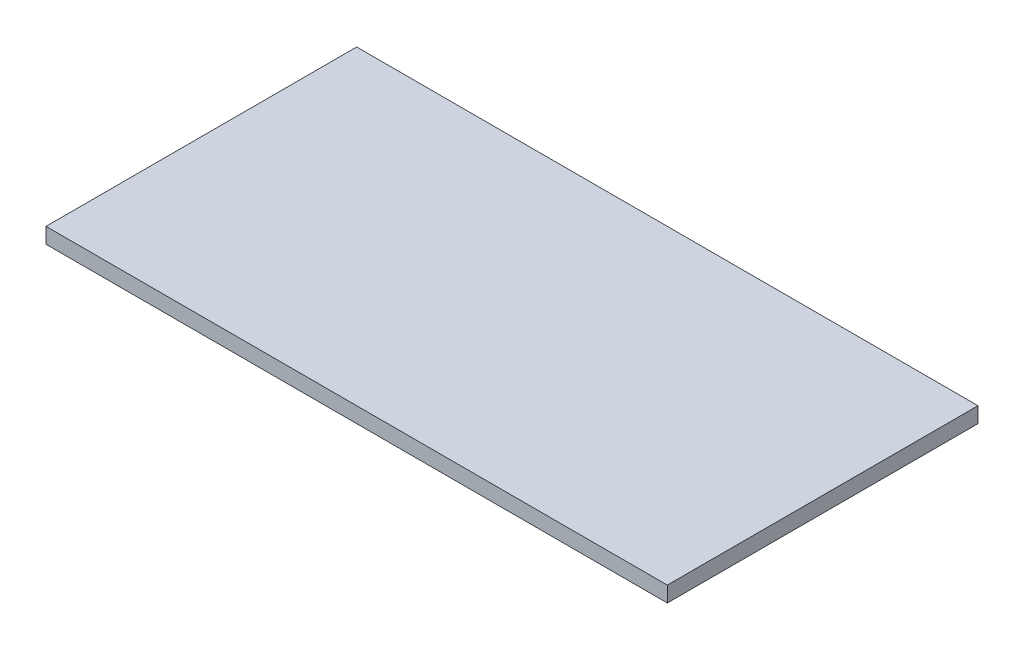
SolidWorks part; units mm, degrees
ref_plane "Front Plane" through (0, 0, 0) normal (0, 0, 1) x (1, 0, 0)
ref_plane "Top Plane" through (0, 0, 0) normal (0, 1, 0) x (1, 0, 0)
ref_plane "Right Plane" through (0, 0, 0) normal (1, 0, 0) x (0, 0, -1)
sketch "Sketch1" plane through (0, 0, 0) normal (0, 1, 0) x (1, 0, 0)
  line L1 (-100, -50) -> (100, -50)
  line L2 (-100, -50) -> (-100, 50)
  line L3 (-100, 50) -> (100, 50)
  line L4 (100, -50) -> (100, 50)
  line L5 (-100, -50) -> (100, 50) construction
  line L6 (-100, 50) -> (100, -50) construction
  point P0 (0, 0)
  dimension "D1" = 200
  dimension "D2" = 100
extrude "Boss-Extrude1" add sketch "Sketch1" along normal blind 5
